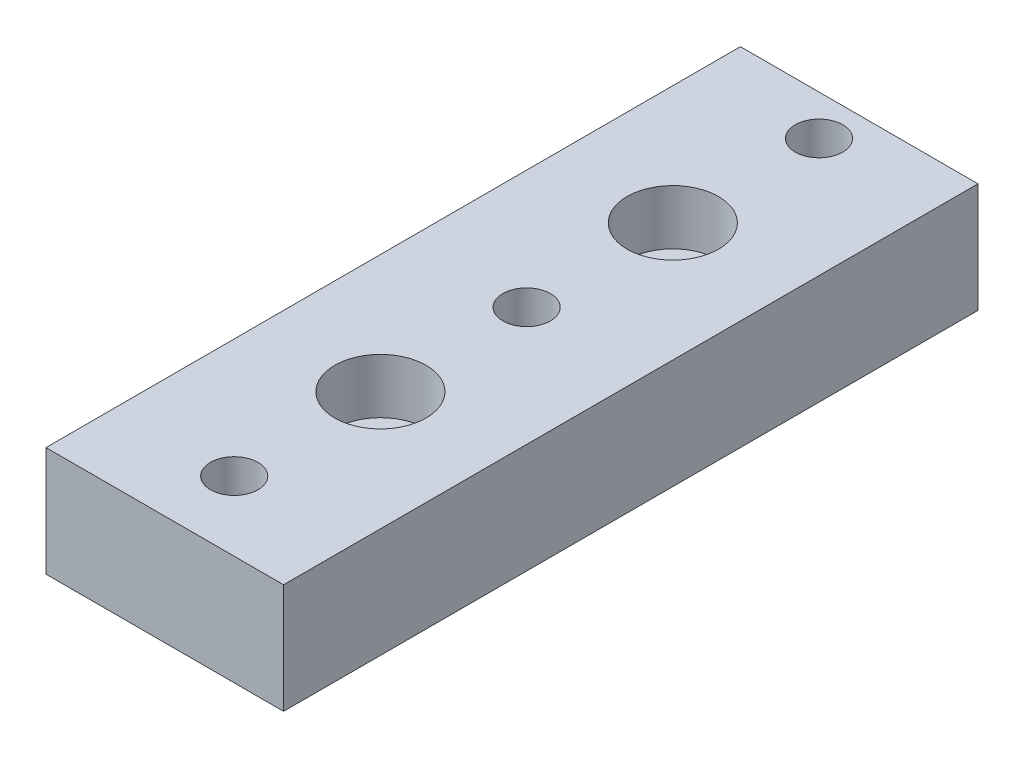
SolidWorks part; units mm, degrees
ref_plane "Front Plane" through (0, 0, 0) normal (0, 0, 1) x (1, 0, 0)
ref_plane "Top Plane" through (0, 0, 0) normal (0, 1, 0) x (1, 0, 0)
ref_plane "Right Plane" through (0, 0, 0) normal (1, 0, 0) x (0, 0, -1)
sketch "Sketch1" plane through (0, 0, 0) normal (0, 1, 0) x (1, 0, 0)
  line L0 (-3.25, -9.5) -> (-3.25, 9.5)
  line L1 (-3.25, -9.5) -> (3.25, -9.5)
  line L2 (-3.25, 9.5) -> (3.25, 9.5)
  line L3 (3.25, -9.5) -> (3.25, 9.5)
  line L4 (-3.25, -9.5) -> (3.25, 9.5) construction
  line L5 (-3.25, 9.5) -> (3.25, -9.5) construction
  point P1 (0, 0)
  dimension "D1" = 19
  dimension "D2" = 6.5
extrude "Boss-Body" add sketch "Sketch1" against normal blind 3
sketch "Sketch2" plane through (0, 0, 0) normal (0, 1, 0) x (1, 0, 0)
  line L0 (0, -1.65) -> (0, 1.65) construction
  line L1 (-3.25, -9.5) -> (3.25, -9.5) construction
  line L2 (0, 8.4) -> (0, 0.4) construction
  line L3 (0, 0.4) -> (0, -7.6) construction
  circle A0 centre (0, -7.6) radius 0.65
  circle A1 centre (0, 0.4) radius 0.65
  circle A2 centre (0, 8.4) radius 0.65
  circle A3 centre (0, 4.4) radius 0.65
  circle A4 centre (0, -3.6) radius 0.65
  dimension "D3" = 1.3
  dimension "D4" = 1.9
  dimension "D1" = 8
  dimension "D2" = 8
extrude "Cut-Screw Holes" cut sketch "Sketch2" against normal through all
sketch "Sketch4" plane through (0, 0, 0) normal (0, 1, 0) x (1, 0, 0)
  circle A0 centre (0, 4.4) radius 1.25
  circle A1 centre (0, -3.6) radius 1.25
  dimension "D1" = 2.5
extrude "Cut-Screw Head Pockets" cut sketch "Sketch4" against normal blind 1.5
